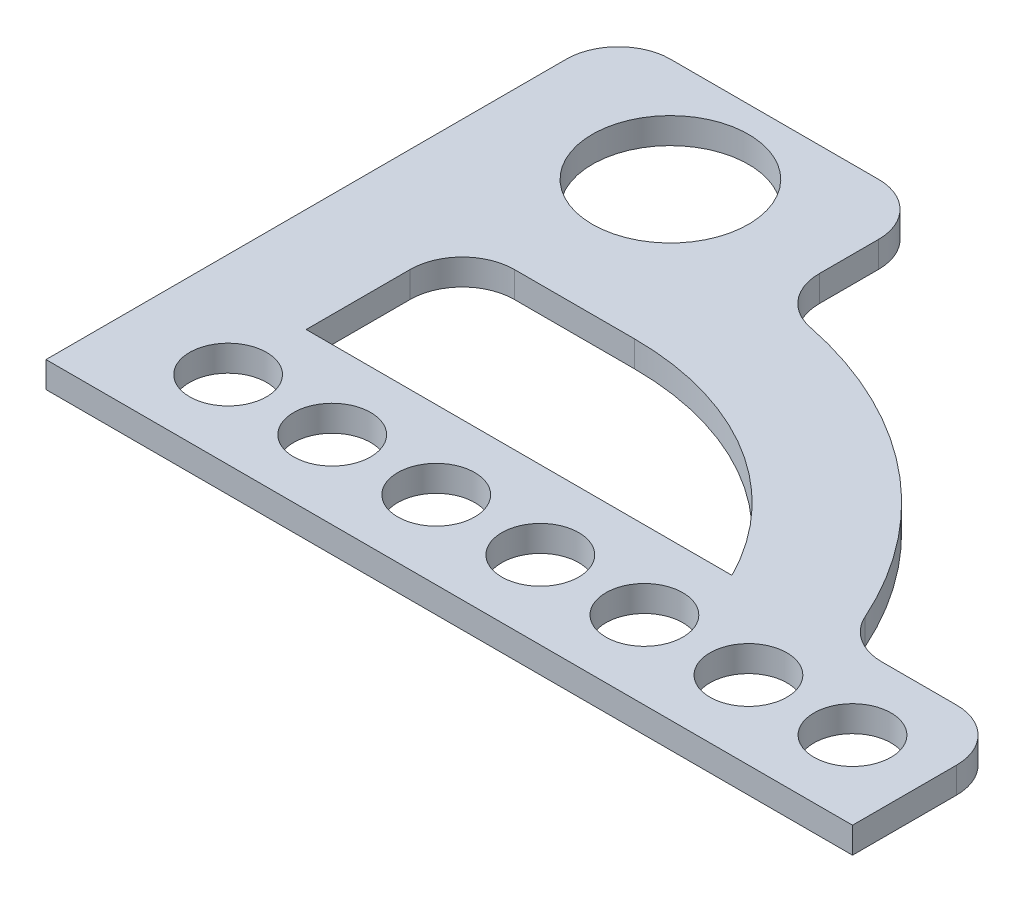
SolidWorks part; units mm, degrees
ref_plane "Front Plane" through (0, 0, 0) normal (0, 0, 1) x (1, 0, 0)
ref_plane "Top Plane" through (0, 0, 0) normal (0, 1, 0) x (1, 0, 0)
ref_plane "Right Plane" through (0, 0, 0) normal (1, 0, 0) x (0, 0, -1)
sketch "Sketch1" plane through (0, 0, 0) normal (0, 1, 0) x (1, 0, 0)
  line L0 (0, 0) -> (0, 100)
  line L1 (10, 110) -> (50, 110)
  line L2 (60, 100) -> (60, 88.6212)
  line L3 (0, 0) -> (155, 0)
  line L4 (155, 0) -> (155, 20)
  line L5 (145, 30) -> (130.6318, 30)
  line L6 (20, 30) -> (101.8301, 30)
  line L7 (101.8301, 30) -> (20, 30)
  line L8 (30, 60) -> (53.1222, 60)
  line L9 (20, 30) -> (20, 50) construction
  line L10 (20, 50) -> (20, 30)
  arc A1 (68.011, 78.821) -> (121.4977, 35.9295) centre (53.1222, 5.4591) cw
  circle A2 centre (30, 90) radius 15
  circle A3 centre (20, 15) radius 7.3968
  arc A4 (53.1222, 60) -> (101.8301, 30) centre (53.1222, 5.4591) cw
  circle A5 centre (40, 15) radius 7.3968
  circle A6 centre (60, 15) radius 7.3968
  circle A7 centre (80, 15) radius 7.3968
  circle A8 centre (100, 15) radius 7.3968
  circle A9 centre (120, 15) radius 7.3968
  circle A10 centre (140, 15) radius 7.3968
  arc A11 (30, 60) -> (20, 50) centre (30, 50) ccw
  arc A12 (0, 100) -> (10, 110) centre (10, 100) cw
  arc A13 (50, 110) -> (60, 100) centre (50, 100) cw
  arc A14 (60, 88.6212) -> (68.011, 78.821) centre (70, 88.6212) ccw
  arc A15 (130.6318, 30) -> (121.4977, 35.9295) centre (130.6318, 40) cw
  arc A16 (155, 20) -> (145, 30) centre (145, 20) ccw
  point P21 (30, 110)
  point P33 (20, 60)
  point P36 (0, 110)
  point P39 (60, 110)
  point P42 (60, 80)
  point P43 (0, 0)
  point P46 (123.8428, 30)
  point P49 (155, 30)
  dimension "D4" = 30
  dimension "D7" = 30
  dimension "D9" = 30
  dimension "D10" = 20
  dimension "D11" = 20
  dimension "D12" = 10
  dimension "D13" = 10
  dimension "D14" = 10
  dimension "D15" = 10
  dimension "D1" = 110
  dimension "D2" = 60
  dimension "D3" = 30
  dimension "D5" = 30
  dimension "D6" = 155
  dimension "D8" = 30
extrude "Boss-Extrude1" add sketch "Sketch1" along normal blind 5 contours L4 A16 L5 A15 A1 A14 L2 A13 L1 A12 L0 L3 A2 A3 A5 A6 A7 A8 A9 A10 A11 L8 A4 L6 L10
